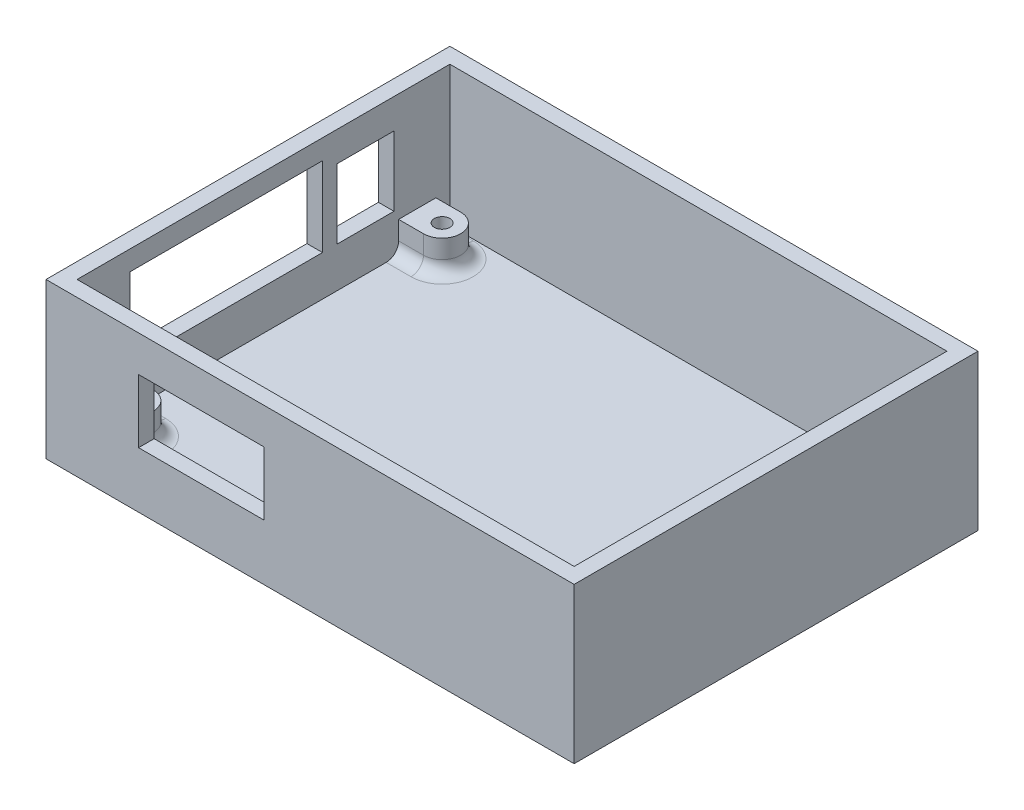
SolidWorks part; units mm, degrees
ref_plane "前视基准面" through (0, 0, 0) normal (0, 0, 1) x (1, 0, 0)
ref_plane "上视基准面" through (0, 0, 0) normal (0, 1, 0) x (1, 0, 0)
ref_plane "右视基准面" through (0, 0, 0) normal (1, 0, 0) x (0, 0, -1)
sketch "草图1" plane through (0, 0, 0) normal (0, 1, 0) x (1, 0, 0)
  line L1 (-42.5, -32.5) -> (42.5, -32.5)
  line L2 (-42.5, -32.5) -> (-42.5, 32.5)
  line L3 (-42.5, 32.5) -> (42.5, 32.5)
  line L4 (42.5, -32.5) -> (42.5, 32.5)
  line L5 (-42.5, -32.5) -> (42.5, 32.5) construction
  line L6 (-42.5, 32.5) -> (42.5, -32.5) construction
  point P0 (0, 0)
  dimension "D1" = 65
  dimension "D2" = 85
extrude "凸台-拉伸1" add sketch "草图1" along normal blind 25
shell "抽壳1" thickness 2.5
sketch "草图2" plane through (0, 2.5, 0) normal (0, 1, 0) x (1, 0, 0)
  line L0 (-36, 0) -> (32.25, 0) construction
  line L1 (32.25, 24.75) -> (-36, 24.75) construction
  line L2 (32.25, 24.75) -> (32.25, -24.75) construction
  line L3 (32.25, -24.75) -> (-36, -24.75) construction
  line L4 (-36, 24.75) -> (-36, -24.75) construction
  line L5 (-40, 30) -> (-40, -30) construction
  line L6 (-36, 27.75) -> (-40, 27.75)
  line L7 (-36, 21.75) -> (-40, 21.75)
  line L8 (-40, 27.75) -> (-40, 21.75)
  line L9 (-36, -21.75) -> (-40, -21.75)
  line L10 (-40, -21.75) -> (-40, -27.75)
  line L11 (-40, 30) -> (-40, -30) construction
  line L12 (-40, -27.75) -> (-36, -27.75)
  arc A0 (-36, 21.75) -> (-36, 27.75) centre (-36, 24.75) ccw
  circle A1 centre (32.25, 24.75) radius 3
  circle A2 centre (32.25, -24.75) radius 3
  arc A3 (-36, -27.75) -> (-36, -21.75) centre (-36, -24.75) ccw
  circle A4 centre (32.25, 24.75) radius 1.25
  circle A5 centre (32.25, -24.75) radius 1.25
  circle A6 centre (-36, -24.75) radius 1.25
  circle A7 centre (-36, 24.75) radius 1.25
  dimension "D4" = 6
  dimension "D5" = 2.5
  dimension "D1" = 49.5
  dimension "D2" = 68.25
  dimension "D3" = 4
extrude "凸台-拉伸2" add sketch "草图2" along normal blind 5
sketch "草图3" plane through (0, 0, 30) normal (0, 0, -1) x (-1, 0, 0)
  line L1 (27.6, 19.2) -> (7.4, 19.2)
  line L2 (27.6, 19.2) -> (27.6, 9)
  line L3 (27.6, 9) -> (7.4, 9)
  line L4 (7.4, 19.2) -> (7.4, 9)
  line L6 (27.6, 19.2) -> (7.4, 9) construction
  line L7 (7.4, 19.2) -> (27.6, 9) construction
  line L8 (40, 25) -> (40, 2.5) construction
  line L9 (40, 2.5) -> (-40, 2.5) construction
  point P4 (17.5, 14.1)
  dimension "D1" = 20.2
  dimension "D2" = 10.2
  dimension "D3" = 22.5
  dimension "D4" = 11.6
extrude "切除-拉伸1" cut sketch "草图3" against normal through all
sketch "草图4" plane through (-40, 0, 0) normal (1, 0, 0) x (0, 0, -1)
  line L1 (21, 20.2) -> (11.8, 20.2)
  line L2 (21, 20.2) -> (21, 9)
  line L3 (21, 9) -> (11.8, 9)
  line L4 (11.8, 20.2) -> (11.8, 9)
  line L5 (9.5, 21.8) -> (-21.5, 21.8)
  line L6 (9.5, 21.8) -> (9.5, 9)
  line L7 (9.5, 9) -> (-21.5, 9)
  line L8 (-21.5, 21.8) -> (-21.5, 9)
  line L11 (9.5, 21.8) -> (-21.5, 9) construction
  line L12 (-21.5, 21.8) -> (9.5, 9) construction
  line L13 (11.8, 20.2) -> (21, 9) construction
  line L14 (21, 20.2) -> (11.8, 9) construction
  line L15 (21.75, 2.5) -> (-21.75, 2.5) construction
  line L16 (30, 25) -> (30, 2.5) construction
  line L17 (-30, 25) -> (-30, 2.5) construction
  point P10 (-6, 15.4)
  point P12 (16.4, 14.6)
  dimension "D1" = 9.2
  dimension "D2" = 11.2
  dimension "D3" = 12.8
  dimension "D4" = 31
  dimension "D5" = 13.6
  dimension "D6" = 24
  dimension "D7" = 12.1
extrude "切除-拉伸2" cut sketch "草图4" against normal through all
fillet "圆角1" radius 2 8 edges at (32.25, 2.5, -27.75) (32.25, 2.5, 21.75) (-38, 2.5, -21.75) (-38, 2.5, -27.75) (-38, 2.5, 27.75) (-38, 2.5, 21.75) (-33, 2.5, -24.75) (-33, 2.5, 24.75)
